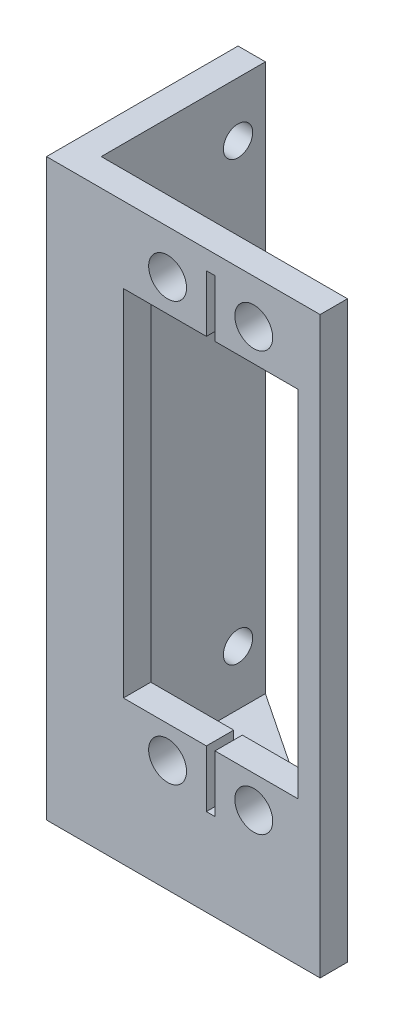
SolidWorks part; units mm, degrees
ref_plane "Front Plane" through (0, 0, 0) normal (0, 0, 1) x (1, 0, 0)
ref_plane "Top Plane" through (0, 0, 0) normal (0, 1, 0) x (1, 0, 0)
ref_plane "Right Plane" through (0, 0, 0) normal (1, 0, 0) x (0, 0, -1)
sketch "Sketch2" plane through (0, 0, 0) normal (0, 0, 1) x (1, 0, 0)
  line L1 (0, 0) -> (31.75, 0)
  line L2 (0, 0) -> (0, 63.5)
  line L3 (0, 63.5) -> (31.75, 63.5)
  line L4 (31.75, 0) -> (31.75, 63.5)
  dimension "D1" = 63.5
  dimension "D2" = 31.75
extrude "Boss-Extrude1" add sketch "Sketch2" along normal blind 3.175 contours L4 L3 L2 L1
sketch "Sketch3" plane through (0, 0, 3.175) normal (0, 0, 1) x (1, 0, 0)
  line L0 (8.923, 54.704) -> (29.177, 13.55) construction
  line L1 (8.923, 54.704) -> (18.55, 54.704)
  line L2 (8.923, 54.704) -> (8.923, 13.55)
  line L3 (8.923, 13.55) -> (18.55, 13.55)
  line L4 (29.177, 54.704) -> (29.177, 13.55)
  line L5 (29.177, 54.704) -> (8.923, 13.55) construction
  line L6 (14.05, 58.427) -> (24.05, 9.827) construction
  line L7 (14.05, 9.827) -> (24.05, 58.427) construction
  line L8 (19.55, 13.55) -> (29.177, 13.55)
  line L9 (18.55, 13.55) -> (18.55, 6.946)
  line L10 (18.55, 6.946) -> (19.55, 6.946)
  line L11 (19.55, 13.55) -> (19.55, 6.946)
  line L12 (19.05, 34.127) -> (62.1329, 34.127) construction
  line L13 (18.55, 61.308) -> (19.55, 61.308)
  line L14 (18.55, 54.704) -> (18.55, 61.308)
  line L15 (19.55, 54.704) -> (19.55, 61.308)
  line L16 (19.55, 54.704) -> (29.177, 54.704)
  line L17 (0, 0) -> (0, 63.5) construction
  line L18 (0, 63.5) -> (31.75, 63.5) construction
  circle A0 centre (14.05, 9.827) radius 2.2
  circle A1 centre (24.05, 9.827) radius 2.2
  circle A2 centre (14.05, 58.427) radius 2.2
  circle A3 centre (24.05, 58.427) radius 2.2
  point P8 (19.05, 6.946)
  point P17 (19.05, 34.127)
  point P18 (19.05, 34.127)
  point P27 (19.05, 44.45)
  dimension "D3" = 4.4
  dimension "D1" = 10
  dimension "D2" = 48.6
  dimension "D4" = 41.154
  dimension "D5" = 20.254
  dimension "D6" = 1
  dimension "D7" = 6.604
  dimension "D8" = 30.9
  dimension "D9" = 19.05
  dimension "D10" = 19.05
extrude "Cut-Extrude1" cut sketch "Sketch3" against normal through all
sketch "Sketch4" plane through (0, 0, 3.175) normal (0, 0, 1) x (1, 0, 0)
  line L0 (0, 0) -> (31.75, 0) construction
  line L1 (0, 63.5) -> (3.175, 63.5)
  line L2 (0, 63.5) -> (0, 0)
  line L3 (0, 0) -> (3.175, 0)
  line L4 (3.175, 63.5) -> (3.175, 0)
  dimension "D1" = 3.175
extrude "Boss-Extrude2" add sketch "Sketch4" against normal blind 19.05 from surface at -3.175 starting at face at (26.25, 9.827, 0)
sketch "Sketch5" plane through (0, 0, 0) normal (0, -1, 0) x (1, 0, 0)
  line L0 (0, 3.175) -> (31.75, 3.175)
  line L1 (31.75, 3.175) -> (31.75, 0)
  line L2 (31.75, 0) -> (3.175, -19.05)
  line L3 (3.175, -19.05) -> (0, -19.05)
  line L4 (0, -19.05) -> (0, 3.175)
extrude "Boss-Extrude3" add sketch "Sketch5" along normal blind 3.175
sketch "Sketch6" plane through (3.175, 0, 0) normal (1, 0, 0) x (0, 0, -1)
  line L0 (0, 0) -> (0, 63.5) construction
  line L1 (19.05, 0) -> (19.05, 63.5) construction
  line L2 (19.05, 63.5) -> (0, 63.5) construction
  line L4 (19.05, 0) -> (0, 0) construction
  circle A0 centre (3.175, 57.15) radius 1.7
  circle A1 centre (3.175, 6.35) radius 1.7
  circle A2 centre (15.875, 57.15) radius 1.7
  circle A3 centre (15.875, 6.35) radius 1.7
  dimension "D5" = 3.4
  dimension "D1" = 3.175
  dimension "D2" = 3.175
  dimension "D3" = 6.35
  dimension "D4" = 6.35
extrude "Cut-Extrude2" cut sketch "Sketch6" against normal through all
sketch "Sketch8" plane through (0, 0, 0) normal (0, 0, -1) x (-1, 0, 0)
  line L0 (-19.55, 13.55) -> (-29.177, 13.55) construction
  line L1 (-29.177, 54.704) -> (-19.55, 54.704) construction
  line L2 (-19.55, 61.308) -> (-18.55, 61.308) construction
  point P0 (-19.05, 44.45)
  point P1 (-19.05, 23.804)
  point P8 (-19.05, 61.308)
  dimension "D1" = 30.9
  dimension "D2" = 30.9
equation "\"D8@Sketch3\"=30.9mm"
equation "\"tighttol\" = 0.005in"
equation "\"normtol\" = 0.01in"
equation "\"loosetol\" = 0.02in"
equation "\"D5@Sketch6\"=3.4mm"
equation "\"D3@Sketch3\"=4.4mm"
equation "\"D1@Sketch8\"=30.9mm"
equation "\"D2@Sketch8\"=30.9mm"
